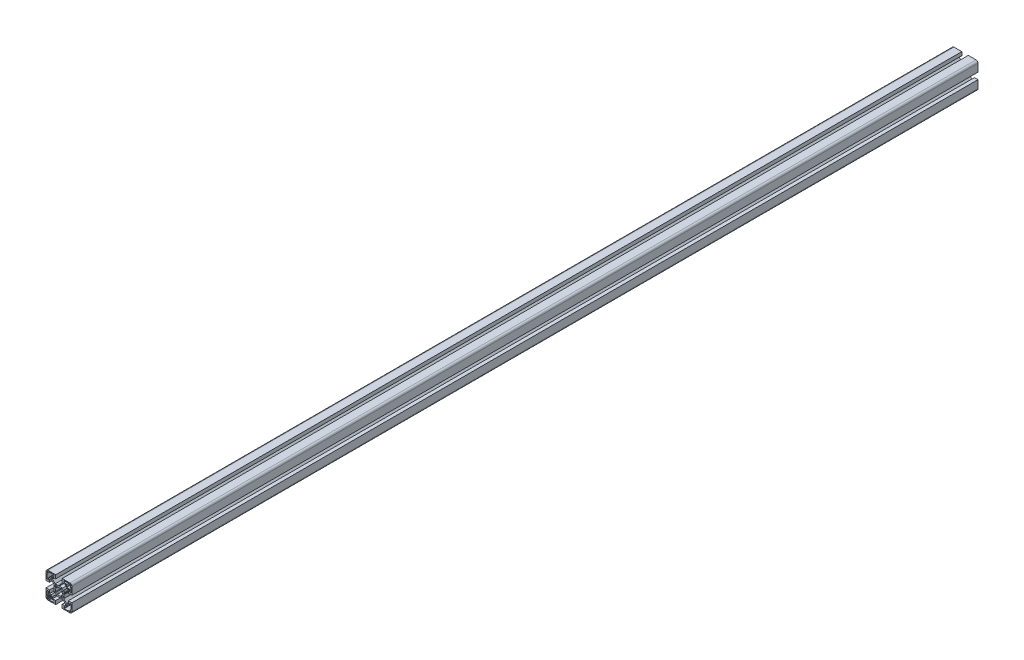
SolidWorks part; units mm, degrees
ref_plane "Front Plane" through (0, 0, 0) normal (0, 0, 1) x (1, 0, 0)
ref_plane "Top Plane" through (0, 0, 0) normal (0, 1, 0) x (1, 0, 0)
ref_plane "Right Plane" through (0, 0, 0) normal (1, 0, 0) x (0, 0, -1)
sketch "Sketch1" plane through (0, 0, 0) normal (0, 0, 1) x (1, 0, 0)
  line L0 (-11.7678, -10) -> (-14.5, -10)
  line L1 (-14.5, -10) -> (-14.5, -5)
  line L2 (-14.5, -5) -> (-20, -5)
  line L3 (-20, -5) -> (-20, -17)
  line L4 (-17, -20) -> (-5, -20)
  line L5 (-5, -20) -> (-5, -14.5)
  line L6 (-5, -14.5) -> (-10, -14.5)
  line L7 (-10, -14.5) -> (-10, -11.7678)
  line L8 (-10, -11.7678) -> (-5.7322, -7.5)
  line L9 (-5.7322, -7.5) -> (-0.6536, -7.5)
  line L10 (-0.4036, -7.433) -> (0, -7.2)
  line L11 (0, -7.2) -> (0.4036, -7.433)
  line L12 (0.9036, -7.433) -> (1.2189, -7.251)
  line L13 (1.2189, -7.251) -> (2.5, -7.5)
  line L14 (2.5, -7.5) -> (5.7322, -7.5)
  line L15 (5.7322, -7.5) -> (10, -11.7678)
  line L16 (10, -11.7678) -> (10, -14.5)
  line L17 (10, -14.5) -> (5, -14.5)
  line L18 (5, -14.5) -> (5, -20)
  line L19 (5, -20) -> (17, -20)
  line L20 (20, -17) -> (20, -5)
  line L21 (20, -5) -> (14.5, -5)
  line L22 (14.5, -5) -> (14.5, -10)
  line L23 (14.5, -10) -> (11.7678, -10)
  line L24 (11.7678, -10) -> (7.5, -5.7322)
  line L25 (7.5, -5.7322) -> (7.5, -0.6536)
  line L26 (7.433, -0.4036) -> (7.2, 0)
  line L27 (7.2, 0) -> (7.433, 0.4036)
  line L28 (7.433, 0.9036) -> (7.251, 1.2189)
  line L29 (7.251, 1.2189) -> (7.5, 2.5)
  line L30 (7.5, 2.5) -> (7.5, 5.7322)
  line L31 (7.5, 5.7322) -> (11.7678, 10)
  line L32 (11.7678, 10) -> (14.5, 10)
  line L33 (14.5, 10) -> (14.5, 5)
  line L34 (14.5, 5) -> (20, 5)
  line L35 (20, 5) -> (20, 17)
  line L36 (17, 20) -> (5, 20)
  line L37 (5, 20) -> (5, 14.5)
  line L38 (5, 14.5) -> (10, 14.5)
  line L39 (10, 14.5) -> (10, 11.7678)
  line L40 (10, 11.7678) -> (5.7322, 7.5)
  line L41 (5.7322, 7.5) -> (0.6536, 7.5)
  line L42 (0.4036, 7.433) -> (0, 7.2)
  line L43 (0, 7.2) -> (-0.4036, 7.433)
  line L44 (-0.9036, 7.433) -> (-1.2189, 7.251)
  line L45 (-1.2189, 7.251) -> (-2.5, 7.5)
  line L46 (-2.5, 7.5) -> (-5.7322, 7.5)
  line L47 (-5.7322, 7.5) -> (-10, 11.7678)
  line L48 (-10, 11.7678) -> (-10, 14.5)
  line L49 (-10, 14.5) -> (-5, 14.5)
  line L50 (-5, 14.5) -> (-5, 20)
  line L51 (-5, 20) -> (-17, 20)
  line L52 (-20, 17) -> (-20, 5)
  line L53 (-20, 5) -> (-14.5, 5)
  line L54 (-14.5, 5) -> (-14.5, 10)
  line L55 (-14.5, 10) -> (-11.7678, 10)
  line L56 (-11.7678, 10) -> (-7.5, 5.7322)
  line L57 (-7.5, 5.7322) -> (-7.5, 0.6536)
  line L58 (-7.433, 0.4036) -> (-7.2, 0)
  line L59 (-7.2, 0) -> (-7.433, -0.4036)
  line L60 (-7.433, -0.9036) -> (-7.251, -1.2189)
  line L61 (-7.251, -1.2189) -> (-7.5, -2.5)
  line L62 (-7.5, -2.5) -> (-7.5, -5.7322)
  line L63 (-7.5, -5.7322) -> (-11.7678, -10)
  line L64 (7.5, 16.5) -> (7.5, 18.2)
  line L65 (8, 18.7) -> (14.8, 18.7)
  line L66 (15, 18.5) -> (15, 18.2)
  line L67 (15.2, 18) -> (16.4, 18)
  line L68 (16.6, 18.2) -> (16.6, 18.5)
  line L69 (16.8, 18.7) -> (17.3, 18.7)
  line L70 (17.6, 18.4) -> (17.6, 17.9)
  line L71 (17.9, 17.6) -> (18.4, 17.6)
  line L72 (18.7, 17.3) -> (18.7, 16.8)
  line L73 (18.5, 16.6) -> (18.2, 16.6)
  line L74 (18, 16.4) -> (18, 15.2)
  line L75 (18.2, 15) -> (18.5, 15)
  line L76 (18.7, 14.8) -> (18.7, 8)
  line L77 (18.2, 7.5) -> (16.5, 7.5)
  line L78 (16, 8) -> (16, 10.2)
  line L79 (14.7, 11.5) -> (12, 11.5)
  line L80 (11.5, 12) -> (11.5, 14.7)
  line L81 (10.2, 16) -> (8, 16)
  line L82 (14.8, -18.7) -> (8, -18.7)
  line L83 (7.5, -18.2) -> (7.5, -16.5)
  line L84 (8, -16) -> (10.2, -16)
  line L85 (11.5, -14.7) -> (11.5, -12)
  line L86 (12, -11.5) -> (14.7, -11.5)
  line L87 (16, -10.2) -> (16, -8)
  line L88 (16.5, -7.5) -> (18.2, -7.5)
  line L89 (18.7, -8) -> (18.7, -14.8)
  line L90 (18.5, -15) -> (18.2, -15)
  line L91 (18, -15.2) -> (18, -16.4)
  line L92 (18.2, -16.6) -> (18.5, -16.6)
  line L93 (18.7, -16.8) -> (18.7, -17.3)
  line L94 (18.4, -17.6) -> (17.9, -17.6)
  line L95 (17.6, -17.9) -> (17.6, -18.4)
  line L96 (17.3, -18.7) -> (16.8, -18.7)
  line L97 (16.6, -18.5) -> (16.6, -18.2)
  line L98 (16.4, -18) -> (15.2, -18)
  line L99 (15, -18.2) -> (15, -18.5)
  line L100 (-18.7, 16.8) -> (-18.7, 17.3)
  line L101 (-18.4, 17.6) -> (-17.9, 17.6)
  line L102 (-17.6, 17.9) -> (-17.6, 18.4)
  line L103 (-17.3, 18.7) -> (-16.8, 18.7)
  line L104 (-16.6, 18.5) -> (-16.6, 18.2)
  line L105 (-16.4, 18) -> (-15.2, 18)
  line L106 (-15, 18.2) -> (-15, 18.5)
  line L107 (-14.8, 18.7) -> (-8, 18.7)
  line L108 (-7.5, 18.2) -> (-7.5, 16.5)
  line L109 (-8, 16) -> (-10.2, 16)
  line L110 (-11.5, 14.7) -> (-11.5, 12)
  line L111 (-12, 11.5) -> (-14.7, 11.5)
  line L112 (-16, 10.2) -> (-16, 8)
  line L113 (-16.5, 7.5) -> (-18.2, 7.5)
  line L114 (-18.7, 8) -> (-18.7, 14.8)
  line L115 (-18.5, 15) -> (-18.2, 15)
  line L116 (-18, 15.2) -> (-18, 16.4)
  line L117 (-18.2, 16.6) -> (-18.5, 16.6)
  line L118 (-18.7, -14.8) -> (-18.7, -8)
  line L119 (-18.2, -7.5) -> (-16.5, -7.5)
  line L120 (-16, -8) -> (-16, -10.2)
  line L121 (-14.7, -11.5) -> (-12, -11.5)
  line L122 (-11.5, -12) -> (-11.5, -14.7)
  line L123 (-10.2, -16) -> (-8, -16)
  line L124 (-7.5, -16.5) -> (-7.5, -18.2)
  line L125 (-8, -18.7) -> (-14.8, -18.7)
  line L126 (-15, -18.5) -> (-15, -18.2)
  line L127 (-15.2, -18) -> (-16.4, -18)
  line L128 (-16.6, -18.2) -> (-16.6, -18.5)
  line L129 (-16.8, -18.7) -> (-17.3, -18.7)
  line L130 (-17.6, -18.4) -> (-17.6, -17.9)
  line L131 (-17.9, -17.6) -> (-18.4, -17.6)
  line L132 (-18.7, -17.3) -> (-18.7, -16.8)
  line L133 (-18.5, -16.6) -> (-18.2, -16.6)
  line L134 (-18, -16.4) -> (-18, -15.2)
  line L135 (-18.2, -15) -> (-18.5, -15)
  line L136 (-6, 3.4907) -> (-6, 5)
  line L137 (-5, 6) -> (-3.4907, 6)
  line L138 (-3.0492, 5.7347) -> (-2.6892, 5.0577)
  line L139 (2.6892, 5.0577) -> (3.0492, 5.7347)
  line L140 (3.4907, 6) -> (5, 6)
  line L141 (6, 5) -> (6, 3.4907)
  line L142 (5.7347, 3.0492) -> (5.0577, 2.6892)
  line L143 (5.0577, -2.6892) -> (5.7347, -3.0492)
  line L144 (6, -3.4907) -> (6, -5)
  line L145 (5, -6) -> (3.4907, -6)
  line L146 (3.0492, -5.7347) -> (2.6892, -5.0577)
  line L147 (-2.6892, -5.0577) -> (-3.0492, -5.7347)
  line L148 (-3.4907, -6) -> (-5, -6)
  line L149 (-6, -5) -> (-6, -3.4907)
  line L150 (-5.7347, -3.0492) -> (-5.0577, -2.6892)
  line L151 (-5.0577, 2.6892) -> (-5.7347, 3.0492)
  arc A0 (-20, -17) -> (-17, -20) centre (-17, -17) ccw
  arc A1 (-0.6536, -7.5) -> (-0.4036, -7.433) centre (-0.6536, -7) ccw
  arc A2 (0.4036, -7.433) -> (0.9036, -7.433) centre (0.6536, -7) ccw
  arc A3 (17, -20) -> (20, -17) centre (17, -17) ccw
  arc A4 (7.5, -0.6536) -> (7.433, -0.4036) centre (7, -0.6536) ccw
  arc A5 (7.433, 0.4036) -> (7.433, 0.9036) centre (7, 0.6536) ccw
  arc A6 (20, 17) -> (17, 20) centre (17, 17) ccw
  arc A7 (0.6536, 7.5) -> (0.4036, 7.433) centre (0.6536, 7) ccw
  arc A8 (-0.4036, 7.433) -> (-0.9036, 7.433) centre (-0.6536, 7) ccw
  arc A9 (-17, 20) -> (-20, 17) centre (-17, 17) ccw
  arc A10 (-7.5, 0.6536) -> (-7.433, 0.4036) centre (-7, 0.6536) ccw
  arc A11 (-7.433, -0.4036) -> (-7.433, -0.9036) centre (-7, -0.6536) ccw
  arc A12 (8, 16) -> (7.5, 16.5) centre (8, 16.5) cw
  arc A13 (7.5, 18.2) -> (8, 18.7) centre (8, 18.2) cw
  arc A14 (14.8, 18.7) -> (15, 18.5) centre (14.8, 18.5) cw
  arc A15 (15, 18.2) -> (15.2, 18) centre (15.2, 18.2) ccw
  arc A16 (16.4, 18) -> (16.6, 18.2) centre (16.4, 18.2) ccw
  arc A17 (16.6, 18.5) -> (16.8, 18.7) centre (16.8, 18.5) cw
  arc A18 (17.3, 18.7) -> (17.6, 18.4) centre (17.3, 18.4) cw
  arc A19 (17.6, 17.9) -> (17.9, 17.6) centre (17.9, 17.9) ccw
  arc A20 (18.4, 17.6) -> (18.7, 17.3) centre (18.4, 17.3) cw
  arc A21 (18.7, 16.8) -> (18.5, 16.6) centre (18.5, 16.8) cw
  arc A22 (18.2, 16.6) -> (18, 16.4) centre (18.2, 16.4) ccw
  arc A23 (18, 15.2) -> (18.2, 15) centre (18.2, 15.2) ccw
  arc A24 (18.5, 15) -> (18.7, 14.8) centre (18.5, 14.8) cw
  arc A25 (18.7, 8) -> (18.2, 7.5) centre (18.2, 8) cw
  arc A26 (16.5, 7.5) -> (16, 8) centre (16.5, 8) cw
  arc A27 (16, 10.2) -> (14.7, 11.5) centre (14.7, 10.2) ccw
  arc A28 (12, 11.5) -> (11.5, 12) centre (12, 12) cw
  arc A29 (11.5, 14.7) -> (10.2, 16) centre (10.2, 14.7) ccw
  arc A30 (8, -18.7) -> (7.5, -18.2) centre (8, -18.2) cw
  arc A31 (7.5, -16.5) -> (8, -16) centre (8, -16.5) cw
  arc A32 (10.2, -16) -> (11.5, -14.7) centre (10.2, -14.7) ccw
  arc A33 (11.5, -12) -> (12, -11.5) centre (12, -12) cw
  arc A34 (14.7, -11.5) -> (16, -10.2) centre (14.7, -10.2) ccw
  arc A35 (16, -8) -> (16.5, -7.5) centre (16.5, -8) cw
  arc A36 (18.2, -7.5) -> (18.7, -8) centre (18.2, -8) cw
  arc A37 (18.7, -14.8) -> (18.5, -15) centre (18.5, -14.8) cw
  arc A38 (18.2, -15) -> (18, -15.2) centre (18.2, -15.2) ccw
  arc A39 (18, -16.4) -> (18.2, -16.6) centre (18.2, -16.4) ccw
  arc A40 (18.5, -16.6) -> (18.7, -16.8) centre (18.5, -16.8) cw
  arc A41 (18.7, -17.3) -> (18.4, -17.6) centre (18.4, -17.3) cw
  arc A42 (17.9, -17.6) -> (17.6, -17.9) centre (17.9, -17.9) ccw
  arc A43 (17.6, -18.4) -> (17.3, -18.7) centre (17.3, -18.4) cw
  arc A44 (16.8, -18.7) -> (16.6, -18.5) centre (16.8, -18.5) cw
  arc A45 (16.6, -18.2) -> (16.4, -18) centre (16.4, -18.2) ccw
  arc A46 (15.2, -18) -> (15, -18.2) centre (15.2, -18.2) ccw
  arc A47 (15, -18.5) -> (14.8, -18.7) centre (14.8, -18.5) cw
  arc A48 (-18.5, 16.6) -> (-18.7, 16.8) centre (-18.5, 16.8) cw
  arc A49 (-18.7, 17.3) -> (-18.4, 17.6) centre (-18.4, 17.3) cw
  arc A50 (-17.9, 17.6) -> (-17.6, 17.9) centre (-17.9, 17.9) ccw
  arc A51 (-17.6, 18.4) -> (-17.3, 18.7) centre (-17.3, 18.4) cw
  arc A52 (-16.8, 18.7) -> (-16.6, 18.5) centre (-16.8, 18.5) cw
  arc A53 (-16.6, 18.2) -> (-16.4, 18) centre (-16.4, 18.2) ccw
  arc A54 (-15.2, 18) -> (-15, 18.2) centre (-15.2, 18.2) ccw
  arc A55 (-15, 18.5) -> (-14.8, 18.7) centre (-14.8, 18.5) cw
  arc A56 (-8, 18.7) -> (-7.5, 18.2) centre (-8, 18.2) cw
  arc A57 (-7.5, 16.5) -> (-8, 16) centre (-8, 16.5) cw
  arc A58 (-10.2, 16) -> (-11.5, 14.7) centre (-10.2, 14.7) ccw
  arc A59 (-11.5, 12) -> (-12, 11.5) centre (-12, 12) cw
  arc A60 (-14.7, 11.5) -> (-16, 10.2) centre (-14.7, 10.2) ccw
  arc A61 (-16, 8) -> (-16.5, 7.5) centre (-16.5, 8) cw
  arc A62 (-18.2, 7.5) -> (-18.7, 8) centre (-18.2, 8) cw
  arc A63 (-18.7, 14.8) -> (-18.5, 15) centre (-18.5, 14.8) cw
  arc A64 (-18.2, 15) -> (-18, 15.2) centre (-18.2, 15.2) ccw
  arc A65 (-18, 16.4) -> (-18.2, 16.6) centre (-18.2, 16.4) ccw
  arc A66 (-18.5, -15) -> (-18.7, -14.8) centre (-18.5, -14.8) cw
  arc A67 (-18.7, -8) -> (-18.2, -7.5) centre (-18.2, -8) cw
  arc A68 (-16.5, -7.5) -> (-16, -8) centre (-16.5, -8) cw
  arc A69 (-16, -10.2) -> (-14.7, -11.5) centre (-14.7, -10.2) ccw
  arc A70 (-12, -11.5) -> (-11.5, -12) centre (-12, -12) cw
  arc A71 (-11.5, -14.7) -> (-10.2, -16) centre (-10.2, -14.7) ccw
  arc A72 (-8, -16) -> (-7.5, -16.5) centre (-8, -16.5) cw
  arc A73 (-7.5, -18.2) -> (-8, -18.7) centre (-8, -18.2) cw
  arc A74 (-14.8, -18.7) -> (-15, -18.5) centre (-14.8, -18.5) cw
  arc A75 (-15, -18.2) -> (-15.2, -18) centre (-15.2, -18.2) ccw
  arc A76 (-16.4, -18) -> (-16.6, -18.2) centre (-16.4, -18.2) ccw
  arc A77 (-16.6, -18.5) -> (-16.8, -18.7) centre (-16.8, -18.5) cw
  arc A78 (-17.3, -18.7) -> (-17.6, -18.4) centre (-17.3, -18.4) cw
  arc A79 (-17.6, -17.9) -> (-17.9, -17.6) centre (-17.9, -17.9) ccw
  arc A80 (-18.4, -17.6) -> (-18.7, -17.3) centre (-18.4, -17.3) cw
  arc A81 (-18.7, -16.8) -> (-18.5, -16.6) centre (-18.5, -16.8) cw
  arc A82 (-18.2, -16.6) -> (-18, -16.4) centre (-18.2, -16.4) ccw
  arc A83 (-18, -15.2) -> (-18.2, -15) centre (-18.2, -15.2) ccw
  arc A84 (-5.7347, 3.0492) -> (-6, 3.4907) centre (-5.5, 3.4907) cw
  arc A85 (-6, 5) -> (-5, 6) centre (-5, 5) cw
  arc A86 (-3.4907, 6) -> (-3.0492, 5.7347) centre (-3.4907, 5.5) cw
  arc A87 (-2.6892, 5.0577) -> (-2.0523, 4.8322) centre (-2.2478, 5.2925) ccw
  arc A88 (-2.0523, 4.8322) -> (2.0523, 4.8322) centre (0, 0) cw
  arc A89 (2.0523, 4.8322) -> (2.6892, 5.0577) centre (2.2478, 5.2925) ccw
  arc A90 (3.0492, 5.7347) -> (3.4907, 6) centre (3.4907, 5.5) cw
  arc A91 (5, 6) -> (6, 5) centre (5, 5) cw
  arc A92 (6, 3.4907) -> (5.7347, 3.0492) centre (5.5, 3.4907) cw
  arc A93 (5.0577, 2.6892) -> (4.8322, 2.0523) centre (5.2925, 2.2478) ccw
  arc A94 (4.8322, 2.0523) -> (4.8322, -2.0523) centre (0, 0) cw
  arc A95 (4.8322, -2.0523) -> (5.0577, -2.6892) centre (5.2925, -2.2478) ccw
  arc A96 (5.7347, -3.0492) -> (6, -3.4907) centre (5.5, -3.4907) cw
  arc A97 (6, -5) -> (5, -6) centre (5, -5) cw
  arc A98 (3.4907, -6) -> (3.0492, -5.7347) centre (3.4907, -5.5) cw
  arc A99 (2.6892, -5.0577) -> (2.0523, -4.8322) centre (2.2478, -5.2925) ccw
  arc A100 (2.0523, -4.8322) -> (-2.0523, -4.8322) centre (0, 0) cw
  arc A101 (-2.0523, -4.8322) -> (-2.6892, -5.0577) centre (-2.2478, -5.2925) ccw
  arc A102 (-3.0492, -5.7347) -> (-3.4907, -6) centre (-3.4907, -5.5) cw
  arc A103 (-5, -6) -> (-6, -5) centre (-5, -5) cw
  arc A104 (-6, -3.4907) -> (-5.7347, -3.0492) centre (-5.5, -3.4907) cw
  arc A105 (-5.0577, -2.6892) -> (-4.8322, -2.0523) centre (-5.2925, -2.2478) ccw
  arc A106 (-4.8322, -2.0523) -> (-4.8322, 2.0523) centre (0, 0) cw
  arc A107 (-4.8322, 2.0523) -> (-5.0577, 2.6892) centre (-5.2925, 2.2478) ccw
extrude "Boss-Extrude1" add sketch "Sketch1" against normal blind 1400
